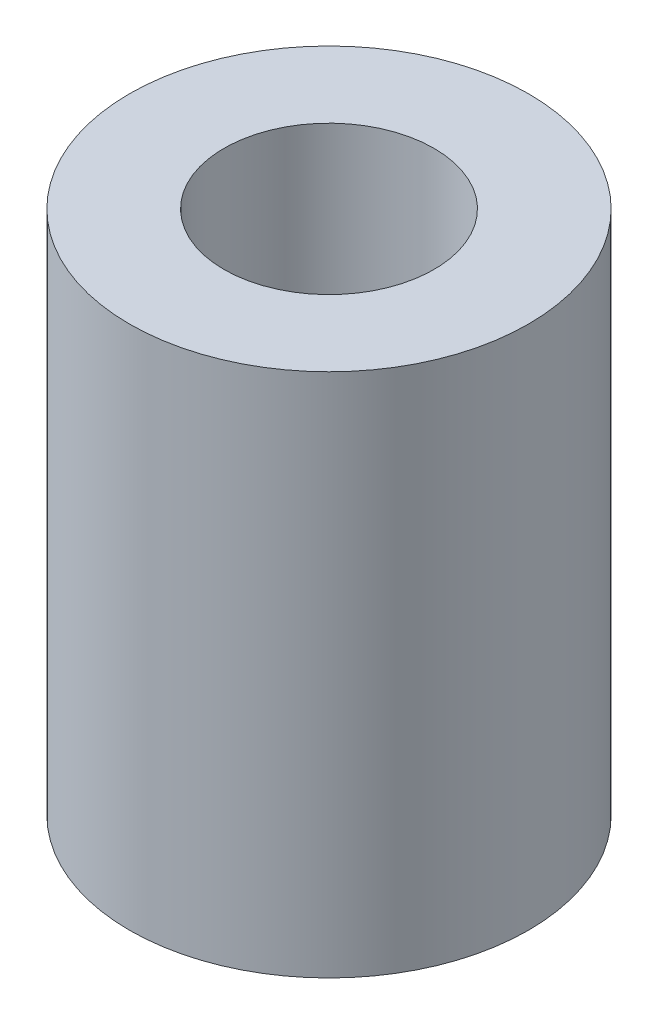
SolidWorks part; units mm, degrees
ref_plane "Front Plane" through (0, 0, 0) normal (0, 0, 1) x (1, 0, 0)
ref_plane "Top Plane" through (0, 0, 0) normal (0, 1, 0) x (1, 0, 0)
ref_plane "Right Plane" through (0, 0, 0) normal (1, 0, 0) x (0, 0, -1)
sketch "Sketch1" plane through (0, 0, 0) normal (0, 1, 0) x (1, 0, 0)
  circle A0 centre (0, 0) radius 9.5
  circle A1 centre (0, 0) radius 5
  dimension "D1" = 19
  dimension "D2" = 10
extrude "Boss-Extrude1" add sketch "Sketch1" along normal blind 25
